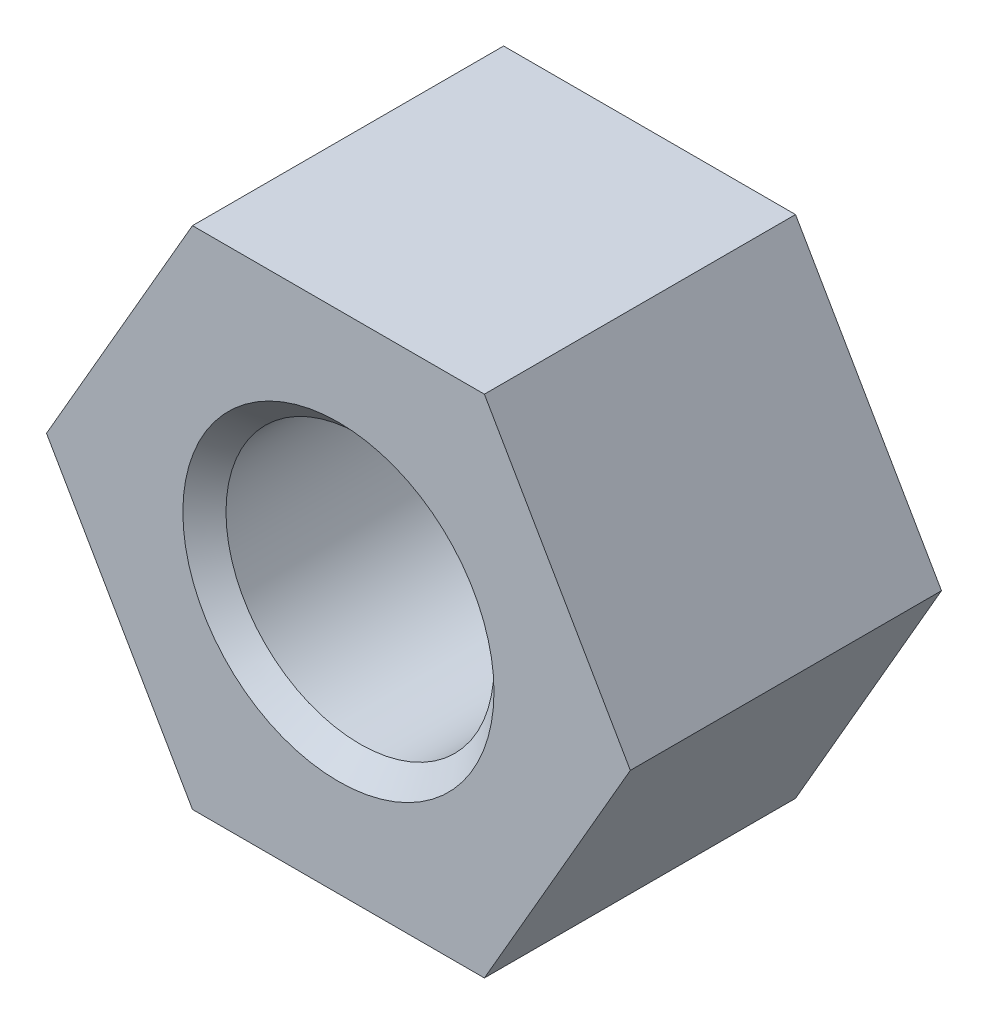
SolidWorks part; units mm, degrees
material "Сталь"
ref_plane "Спереди" through (0, 0, 0) normal (0, 0, 1) x (1, 0, 0)
ref_plane "Сверху" through (0, 0, 0) normal (0, 1, 0) x (1, 0, 0)
ref_plane "Справа" through (0, 0, 0) normal (1, 0, 0) x (0, 0, -1)
sketch "Эскиз1" plane through (0, 0, 0) normal (0, 0, 1) x (1, 0, 0)
  line L1 (3.7528, 6.5) -> (-3.7528, 6.5)
  line L2 (-3.7528, 6.5) -> (-7.5056, 0)
  line L3 (-7.5056, 0) -> (-3.7528, -6.5)
  line L4 (-3.7528, -6.5) -> (3.7528, -6.5)
  line L5 (3.7528, -6.5) -> (7.5056, 0)
  line L6 (7.5056, 0) -> (3.7528, 6.5)
  circle A0 centre (0, 0) radius 6.5 construction
  circle A1 centre (0, 0) radius 3.4455
  dimension "D2" = 6.891
  dimension "D1" = 13
extrude "Бобышка-Вытянуть1" add sketch "Эскиз1" along normal blind 8
cosmetic thread "Условное изображение резьбы1" parameters "D1"=8, "D2"=8
chamfer "Фаска1" distance 0.5545 angle 45 2 edges at (3.4455, 0, 0) (3.4455, 0, 8)
